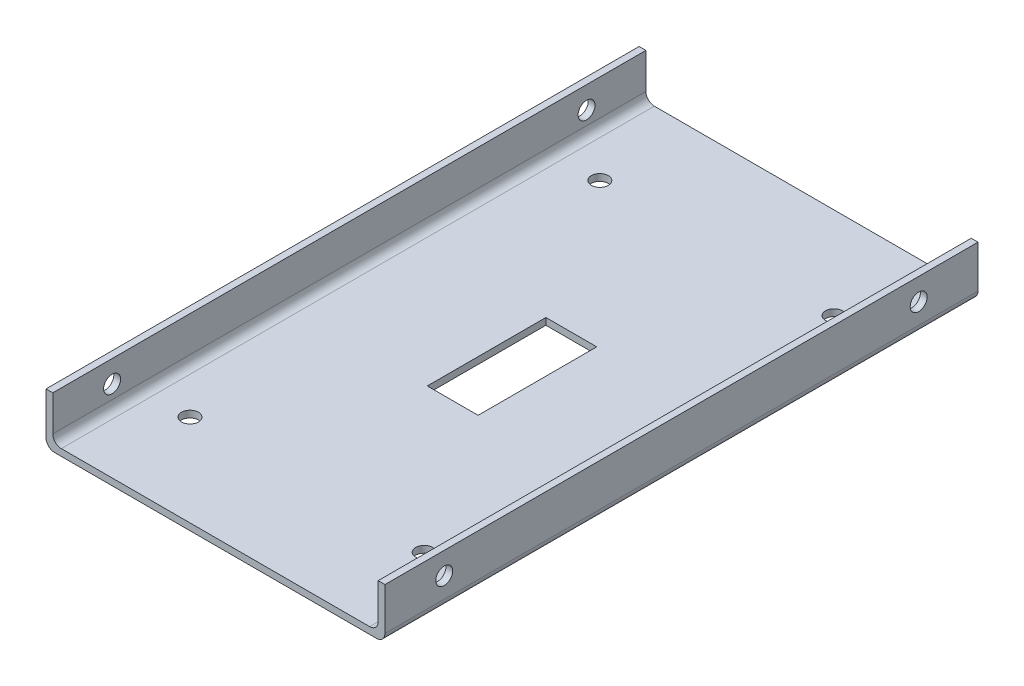
SolidWorks part; units mm, degrees
ref_plane "Front Plane" through (0, 0, 0) normal (0, 0, 1) x (1, 0, 0)
ref_plane "Top Plane" through (0, 0, 0) normal (0, 1, 0) x (1, 0, 0)
ref_plane "Right Plane" through (0, 0, 0) normal (1, 0, 0) x (0, 0, -1)
sketch "Sketch1" plane through (0, 0, 0) normal (0, 0, 1) x (1, 0, 0)
  line L0 (0, 0) -> (200, 0)
  line L1 (200, 30) -> (200, 0)
  line L2 (0, 30) -> (0, 0)
  line L3 (0, 30) -> (4, 30)
  line L4 (4, 4) -> (196, 4)
  line L5 (196, 4) -> (196, 30)
  line L6 (196, 30) -> (200, 30)
  line L7 (4, 30) -> (4, 4)
  dimension "D1" = 4
  dimension "D2" = 4
  dimension "D3" = 30
  dimension "D4" = 200
  dimension "D5" = 4
extrude "Boss-Extrude1" add sketch "Sketch1" along normal blind 350
fillet "Fillet1" radius 5 4 edges at (4, 4, 175) (0, 0, 175) (200, 0, 175) (196, 4, 175)
sketch "Sketch2" plane through (200, 0, 0) normal (1, 0, 0) x (0, 0, -1)
  line L0 (-350, 30) -> (0, 30) construction
  line L2 (0, 0) -> (-350, 0) construction
  line L3 (-350, 5) -> (-350, 30) construction
  circle A0 centre (-315, 17) radius 5
  circle A1 centre (-35, 17) radius 5
  dimension "D1" = 10
  dimension "D2" = 280
  dimension "D3" = 17
  dimension "D4" = 35
extrude "Cut-Extrude1" cut sketch "Sketch2" against normal blind 300
sketch "Sketch3" plane through (0, 0, 0) normal (0, 1, 0) x (1, 0, 0)
  line L0 (0, 0) -> (200, -350) construction
  line L1 (0, -350) -> (200, 0) construction
  line L3 (115, -140) -> (85, -140)
  line L4 (115, -140) -> (115, -210)
  line L5 (115, -210) -> (85, -210)
  line L6 (85, -140) -> (85, -210)
  line L7 (115, -140) -> (85, -210) construction
  line L8 (115, -210) -> (85, -140) construction
  circle A0 centre (30.8949, -54.0661) radius 5
  circle A1 centre (169.1051, -54.0661) radius 5
  circle A2 centre (169.1051, -295.9339) radius 5
  circle A3 centre (30.8949, -295.9339) radius 5
  point P16 (100, -175)
  dimension "D1" = 10
  dimension "D2" = 120
  dimension "D3" = 70
  dimension "D4" = 30
extrude "Cut-Extrude6" cut sketch "Sketch3" along normal blind 10
